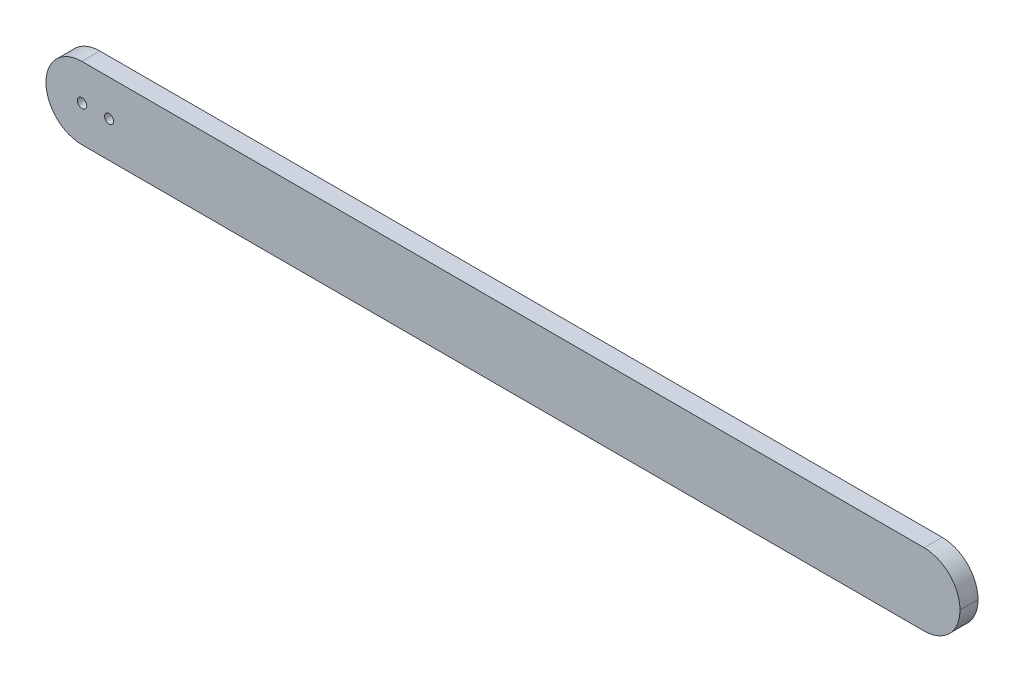
SolidWorks part; units mm, degrees
ref_plane "Front Plane" through (0, 0, 0) normal (0, 0, 1) x (1, 0, 0)
ref_plane "Top Plane" through (0, 0, 0) normal (0, 1, 0) x (1, 0, 0)
ref_plane "Right Plane" through (0, 0, 0) normal (1, 0, 0) x (0, 0, -1)
sketch "Sketch2" plane through (0, 0, 0) normal (0, 0, 1) x (1, 0, 0)
  line L1 (37.846, 0) -> (927.354, 0)
  line L2 (0, -37.846) -> (0, -38.354)
  line L3 (37.846, -76.2) -> (927.354, -76.2)
  line L4 (965.2, -37.846) -> (965.2, -38.354)
  arc A0 (965.2, -38.354) -> (927.354, -76.2) centre (927.354, -38.354) cw
  arc A1 (965.2, -37.846) -> (927.354, 0) centre (927.354, -37.846) ccw
  arc A2 (0, -38.354) -> (37.846, -76.2) centre (37.846, -38.354) ccw
  arc A3 (0, -37.846) -> (37.846, 0) centre (37.846, -37.846) cw
  point P9 (965.2, 0)
  point P14 (0, 0)
  dimension "D3" = 37.846
  dimension "D1" = 76.2
  dimension "D2" = 965.2
extrude "Boss-Extrude1" add sketch "Sketch2" along normal blind 19.05
sketch "Sketch3" plane through (0, 0, 0) normal (0, 0, 1) x (1, 0, 0)
  line L0 (965.2, -38.1) -> (0, -38.1) construction
  line L1 (965.2, -38.354) -> (965.2, -37.846) construction
  line L2 (0, -37.846) -> (0, -38.354) construction
  line L3 (844.55, 16.355) -> (844.55, -92.9933) construction
  line L4 (723.9, 16.355) -> (723.9, -92.9933) construction
  line L5 (603.25, 16.355) -> (603.25, -92.9933) construction
  line L6 (482.6, 16.355) -> (482.6, -92.9933) construction
  line L7 (361.95, 16.355) -> (361.95, -92.9933) construction
  line L8 (241.3, 16.355) -> (241.3, -92.9933) construction
  line L9 (120.65, 16.355) -> (120.65, -92.9933) construction
  circle A0 centre (844.55, -38.1) radius 16.6687
  circle A1 centre (723.9, -38.1) radius 16.6687
  circle A2 centre (603.25, -38.1) radius 16.6687
  circle A3 centre (482.6, -38.1) radius 16.6687
  circle A4 centre (361.95, -38.1) radius 16.6687
  circle A5 centre (241.3, -38.1) radius 16.6687
  circle A6 centre (120.65, -38.1) radius 16.6687
  dimension "D3" = 7
  dimension "D1" = 120.65
  dimension "D2" = 7
extrude "Cut-Extrude1" cut sketch "Sketch3" along normal blind 9.525 contours A6 | A5 | A4 | A0 | A1 | A2 | A3
sketch "Sketch5" plane through (0, 0, 0) normal (0, 0, 1) x (1, 0, 0)
  line L0 (-1000, -38.1) -> (49000, -38.1) construction
  line L1 (0, -37.846) -> (0, -38.354) construction
  circle A0 centre (38.1, -38.1) radius 4.9609
  circle A1 centre (38.1, -38.1) radius 28.575 construction
  circle A2 centre (66.675, -38.1) radius 4.7625
  point P5 (0, -38.1)
  dimension "D2" = 9.9219
  dimension "D3" = 57.15
  dimension "D4" = 9.525
  dimension "D1" = 38.1
extrude "Cut-Extrude10" cut sketch "Sketch5" along normal blind 19.05
